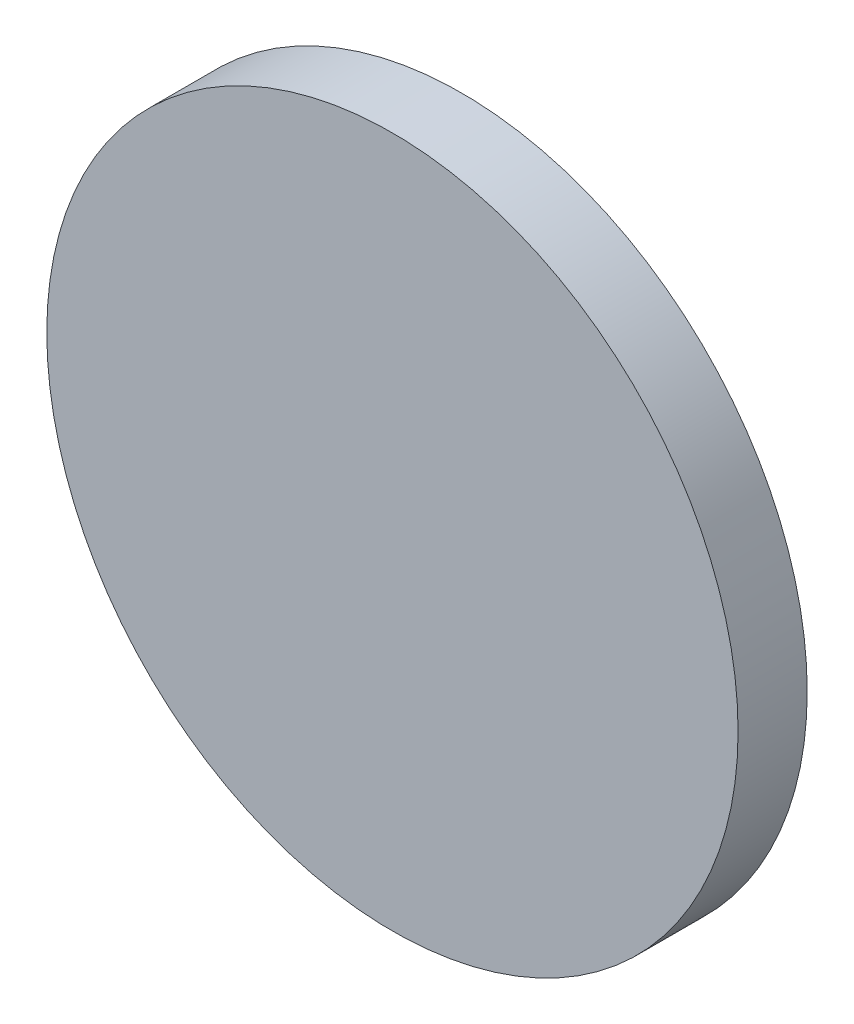
SolidWorks part; units mm, degrees
ref_plane "前视基准面" through (0, 0, 0) normal (0, 0, 1) x (1, 0, 0)
ref_plane "上视基准面" through (0, 0, 0) normal (0, 1, 0) x (1, 0, 0)
ref_plane "右视基准面" through (0, 0, 0) normal (1, 0, 0) x (0, 0, -1)
sketch "草图1" plane through (0, 0, 0) normal (0, 0, 1) x (1, 0, 0)
  circle A0 centre (0, 0) radius 10
  dimension "D1" = 20
extrude "凸台-拉伸1" add sketch "草图1" along normal blind 2 contours A0
